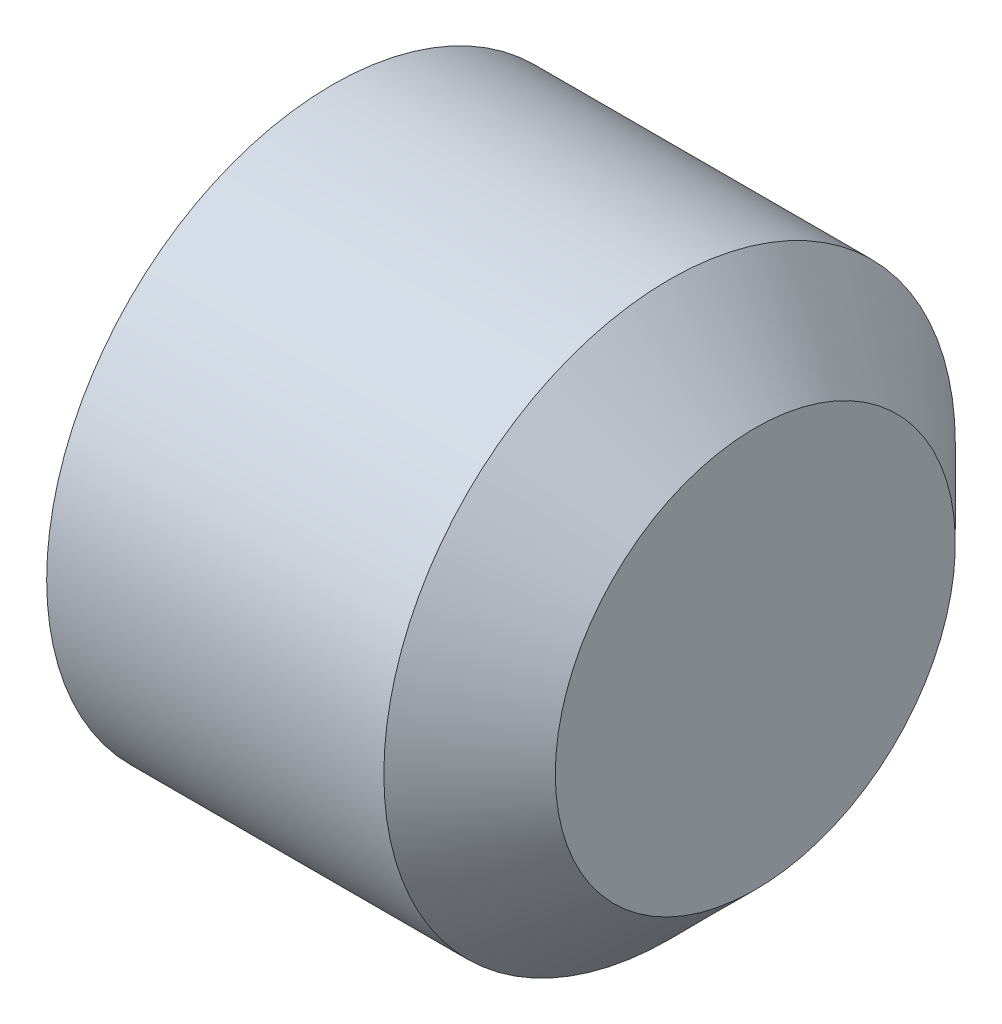
SolidWorks part; units mm, degrees
ref_plane "Front" through (0, 0, 0) normal (0, 0, 1) x (1, 0, 0)
ref_plane "Top" through (0, 0, 0) normal (0, 1, 0) x (1, 0, 0)
ref_plane "Right" through (0, 0, 0) normal (1, 0, 0) x (0, 0, -1)
sketch "Sketch1" plane through (0, 0, 0) normal (0, 0, 1) x (1, 0, 0)
  line L0 (-0.3947, 0) -> (4.5112, 0) construction
  line L2 (0, 2.5) -> (4, 2.5)
  line L3 (0, 2.5) -> (0, 0)
  line L4 (0, 0) -> (4, 0)
  line L5 (4, 2.5) -> (4, 0)
  dimension "D1" = 4
  dimension "D2" = 5
revolve "Revolve1" add sketch "Sketch1" angle 360 about L0
sketch "Sketch2" plane through (0, 0, 0) normal (1, 0, 0) x (0, 0, -1)
  line L7 (-0.7217, 1.25) -> (-1.4434, 0)
  line L8 (-1.4434, 0) -> (-0.7217, -1.25)
  line L9 (-0.7217, -1.25) -> (0.7217, -1.25)
  line L10 (0.7217, -1.25) -> (1.4434, 0)
  line L11 (1.4434, 0) -> (0.7217, 1.25)
  line L12 (0.7217, 1.25) -> (-0.7217, 1.25)
  circle A0 centre (0, 0) radius 1.25 construction
  dimension "D1" = 2.5
extrude "Cut-Extrude1" cut sketch "Sketch2" along normal blind 2
chamfer "Chamfer1" distance 0.75 1 edges at (4, 0, 2.5)
chamfer "Chamfer2" distance 0.3 distance2 0.5 1 edges at (0, 0, 2.5)
